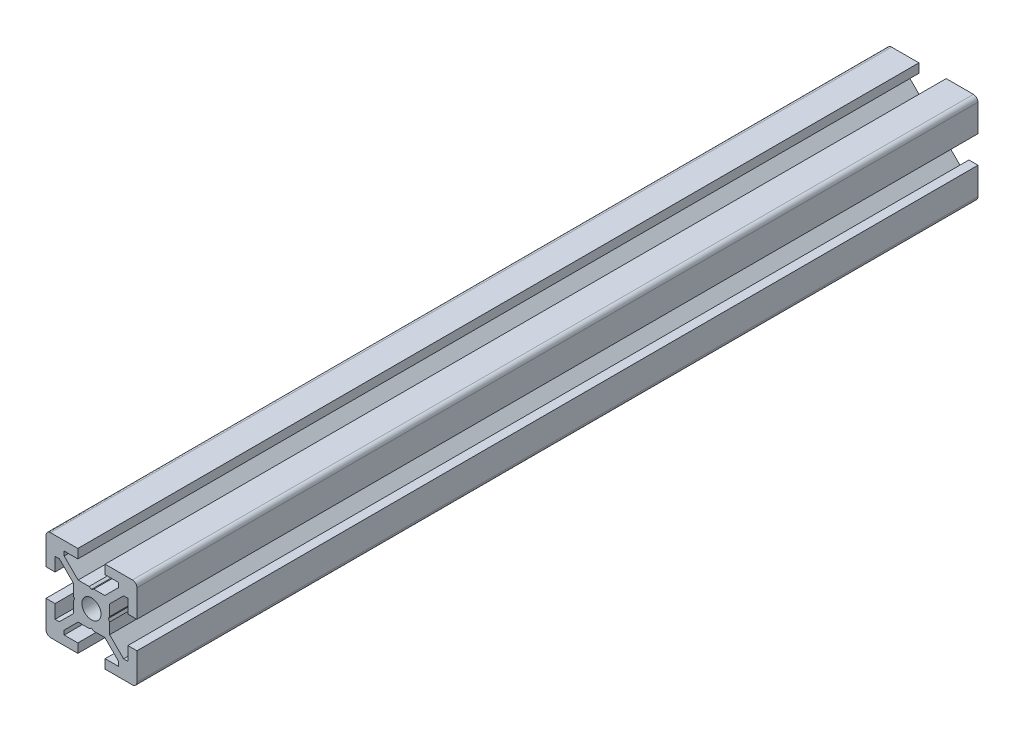
SolidWorks part; units mm, degrees
material "2014 合金"
ref_plane "正面" through (0, 0, 0) normal (0, 0, 1) x (1, 0, 0)
ref_plane "平面" through (0, 0, 0) normal (0, 1, 0) x (1, 0, 0)
ref_plane "右側面" through (0, 0, 0) normal (1, 0, 0) x (0, 0, -1)
ref_plane "平面1" through (0, 0, 0) normal (0, 0, 1) x (1, 0, 0)
sketch "ｽｹｯﾁ1" plane through (0, 0, 0) normal (0, 0, 1) x (1, 0, 0)
  line L0 (-10, -3) -> (-10, -9)
  line L1 (-9, -10) -> (-3, -10)
  line L2 (-3, -10) -> (-3, -8)
  line L3 (-3, -8) -> (-6, -8)
  line L4 (-6, -8) -> (-6, -7.0607)
  line L5 (-6, -7.0607) -> (-2.9393, -4)
  line L6 (-2.9393, -4) -> (-0.5196, -4)
  line L7 (-0.5196, -4) -> (0, -3.7)
  line L8 (0, -3.7) -> (0.5196, -4)
  line L9 (0.5196, -4) -> (2.9393, -4)
  line L10 (2.9393, -4) -> (6, -7.0607)
  line L11 (6, -7.0607) -> (6, -8)
  line L12 (6, -8) -> (3, -8)
  line L13 (3, -8) -> (3, -10)
  line L14 (3, -10) -> (9, -10)
  line L15 (10, -9) -> (10, -3)
  line L16 (10, -3) -> (8, -3)
  line L17 (8, -3) -> (8, -6)
  line L18 (8, -6) -> (7.0607, -6)
  line L19 (7.0607, -6) -> (4, -2.9393)
  line L20 (4, -2.9393) -> (4, -0.5196)
  line L21 (4, -0.5196) -> (3.7, 0)
  line L22 (3.7, 0) -> (4, 0.5196)
  line L23 (4, 0.5196) -> (4, 2.9393)
  line L24 (4, 2.9393) -> (7.0607, 6)
  line L25 (7.0607, 6) -> (8, 6)
  line L26 (8, 6) -> (8, 3)
  line L27 (8, 3) -> (10, 3)
  line L28 (10, 3) -> (10, 9)
  line L29 (9, 10) -> (3, 10)
  line L30 (3, 10) -> (3, 8)
  line L31 (3, 8) -> (6, 8)
  line L32 (6, 8) -> (6, 7.0607)
  line L33 (6, 7.0607) -> (2.9393, 4)
  line L34 (2.9393, 4) -> (0.5196, 4)
  line L35 (0.5196, 4) -> (0, 3.7)
  line L36 (0, 3.7) -> (-0.5196, 4)
  line L37 (-0.5196, 4) -> (-2.9393, 4)
  line L38 (-2.9393, 4) -> (-6, 7.0607)
  line L39 (-6, 7.0607) -> (-6, 8)
  line L40 (-6, 8) -> (-3, 8)
  line L41 (-3, 8) -> (-3, 10)
  line L42 (-3, 10) -> (-9, 10)
  line L43 (-10, 9) -> (-10, 3)
  line L44 (-10, 3) -> (-8, 3)
  line L45 (-8, 3) -> (-8, 6)
  line L46 (-8, 6) -> (-7.0607, 6)
  line L47 (-7.0607, 6) -> (-4, 2.9393)
  line L48 (-4, 2.9393) -> (-4, 0.5196)
  line L49 (-4, 0.5196) -> (-3.7, 0)
  line L50 (-3.7, 0) -> (-4, -0.5196)
  line L51 (-4, -0.5196) -> (-4, -2.9393)
  line L52 (-4, -2.9393) -> (-7.0607, -6)
  line L53 (-7.0607, -6) -> (-8, -6)
  line L54 (-8, -6) -> (-8, -3)
  line L55 (-8, -3) -> (-10, -3)
  arc A0 (-10, -9) -> (-9, -10) centre (-9, -9) ccw
  arc A1 (9, -10) -> (10, -9) centre (9, -9) ccw
  arc A2 (10, 9) -> (9, 10) centre (9, 9) ccw
  arc A3 (-9, 10) -> (-10, 9) centre (-9, 9) ccw
extrude "ﾎﾞｽ - 押し出し1" add sketch "ｽｹｯﾁ1" against normal blind 185
ref_plane "平面2" through (0, 0, 0) normal (1, 0, 0) x (0, 0, -1)
sketch "ｽｹｯﾁ2" plane through (0, 0, 0) normal (1, 0, 0) x (0, 0, -1)
  line L0 (0, 0) -> (0, 2.1)
  line L1 (0, 2.1) -> (260, 2.1)
  line L2 (260, 2.1) -> (260, 0)
  line L3 (260, 0) -> (0, 0)
  line L4 (260, 0) -> (0, 0) construction
revolve "ｶｯﾄ - 回転1" cut sketch "ｽｹｯﾁ2" angle 360 about L4
